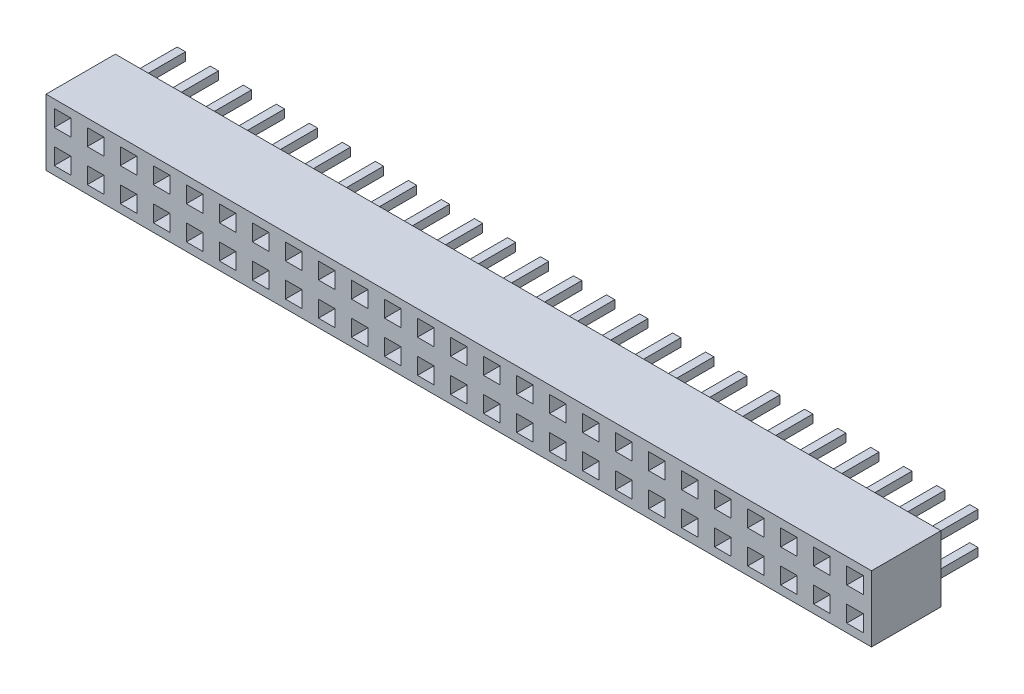
SolidWorks part; units mm, degrees
material "黄銅"
ref_plane "正面" through (0, 0, 0) normal (0, 0, 1) x (1, 0, 0)
ref_plane "平面" through (0, 0, 0) normal (0, 1, 0) x (1, 0, 0)
ref_plane "右側面" through (0, 0, 0) normal (1, 0, 0) x (0, 0, -1)
sketch "Sketch1" plane through (0, 0, 0) normal (0, 0, 1) x (1, 0, 0)
  line L1 (-25, 2) -> (25, 2)
  line L2 (-25, 2) -> (-25, -2)
  line L3 (-25, -2) -> (25, -2)
  line L4 (25, 2) -> (25, -2)
  line L5 (-25, 2) -> (25, -2) construction
  line L6 (-25, -2) -> (25, 2) construction
  point P0 (0, 0)
  dimension "D1" = 50
  dimension "D2" = 4
extrude "Boss-Extrude1" add sketch "Sketch1" along normal blind 4.2
sketch "Sketch3" plane through (0, 0, 4.2) normal (0, 0, 1) x (1, 0, 0)
  line L0 (25, 2) -> (-25, 2) construction
  line L1 (-24.5, 1.5) -> (-23.5, 1.5)
  line L2 (-24.5, 1.5) -> (-24.5, 0.5)
  line L3 (-24.5, 0.5) -> (-23.5, 0.5)
  line L4 (-23.5, 1.5) -> (-23.5, 0.5)
  line L5 (-24.5, -0.5) -> (-23.5, -0.5)
  line L6 (-24.5, -0.5) -> (-24.5, -1.5)
  line L7 (-24.5, -1.5) -> (-23.5, -1.5)
  line L8 (-23.5, -0.5) -> (-23.5, -1.5)
  line L9 (-25, 2) -> (-25, -2) construction
  line L10 (-25, -2) -> (25, -2) construction
  line L11 (-21.5, 1.5) -> (-21.5, 0.5)
  line L12 (-22.5, 1.5) -> (-21.5, 1.5)
  line L13 (-22.5, 1.5) -> (-22.5, 0.5)
  line L14 (-22.5, 0.5) -> (-21.5, 0.5)
  line L15 (-19.5, 1.5) -> (-19.5, 0.5)
  line L16 (-20.5, 1.5) -> (-19.5, 1.5)
  line L17 (-20.5, 1.5) -> (-20.5, 0.5)
  line L18 (-20.5, 0.5) -> (-19.5, 0.5)
  line L19 (-17.5, 1.5) -> (-17.5, 0.5)
  line L20 (-18.5, 1.5) -> (-17.5, 1.5)
  line L21 (-18.5, 1.5) -> (-18.5, 0.5)
  line L22 (-18.5, 0.5) -> (-17.5, 0.5)
  line L23 (-15.5, 1.5) -> (-15.5, 0.5)
  line L24 (-16.5, 1.5) -> (-15.5, 1.5)
  line L25 (-16.5, 1.5) -> (-16.5, 0.5)
  line L26 (-16.5, 0.5) -> (-15.5, 0.5)
  line L27 (-13.5, 1.5) -> (-13.5, 0.5)
  line L28 (-14.5, 1.5) -> (-13.5, 1.5)
  line L29 (-14.5, 1.5) -> (-14.5, 0.5)
  line L30 (-14.5, 0.5) -> (-13.5, 0.5)
  line L31 (-11.5, 1.5) -> (-11.5, 0.5)
  line L32 (-12.5, 1.5) -> (-11.5, 1.5)
  line L33 (-12.5, 1.5) -> (-12.5, 0.5)
  line L34 (-12.5, 0.5) -> (-11.5, 0.5)
  line L35 (-9.5, 1.5) -> (-9.5, 0.5)
  line L36 (-10.5, 1.5) -> (-9.5, 1.5)
  line L37 (-10.5, 1.5) -> (-10.5, 0.5)
  line L38 (-10.5, 0.5) -> (-9.5, 0.5)
  line L39 (-7.5, 1.5) -> (-7.5, 0.5)
  line L40 (-8.5, 1.5) -> (-7.5, 1.5)
  line L41 (-8.5, 1.5) -> (-8.5, 0.5)
  line L42 (-8.5, 0.5) -> (-7.5, 0.5)
  line L43 (-5.5, 1.5) -> (-5.5, 0.5)
  line L44 (-6.5, 1.5) -> (-5.5, 1.5)
  line L45 (-6.5, 1.5) -> (-6.5, 0.5)
  line L46 (-6.5, 0.5) -> (-5.5, 0.5)
  line L47 (-3.5, 1.5) -> (-3.5, 0.5)
  line L48 (-4.5, 1.5) -> (-3.5, 1.5)
  line L49 (-4.5, 1.5) -> (-4.5, 0.5)
  line L50 (-4.5, 0.5) -> (-3.5, 0.5)
  line L51 (-1.5, 1.5) -> (-1.5, 0.5)
  line L52 (-2.5, 1.5) -> (-1.5, 1.5)
  line L53 (-2.5, 1.5) -> (-2.5, 0.5)
  line L54 (-2.5, 0.5) -> (-1.5, 0.5)
  line L55 (0.5, 1.5) -> (0.5, 0.5)
  line L56 (-0.5, 1.5) -> (0.5, 1.5)
  line L57 (-0.5, 1.5) -> (-0.5, 0.5)
  line L58 (-0.5, 0.5) -> (0.5, 0.5)
  line L59 (2.5, 1.5) -> (2.5, 0.5)
  line L60 (1.5, 1.5) -> (2.5, 1.5)
  line L61 (1.5, 1.5) -> (1.5, 0.5)
  line L62 (1.5, 0.5) -> (2.5, 0.5)
  line L63 (4.5, 1.5) -> (4.5, 0.5)
  line L64 (3.5, 1.5) -> (4.5, 1.5)
  line L65 (3.5, 1.5) -> (3.5, 0.5)
  line L66 (3.5, 0.5) -> (4.5, 0.5)
  line L67 (6.5, 1.5) -> (6.5, 0.5)
  line L68 (5.5, 1.5) -> (6.5, 1.5)
  line L69 (5.5, 1.5) -> (5.5, 0.5)
  line L70 (5.5, 0.5) -> (6.5, 0.5)
  line L71 (8.5, 1.5) -> (8.5, 0.5)
  line L72 (7.5, 1.5) -> (8.5, 1.5)
  line L73 (7.5, 1.5) -> (7.5, 0.5)
  line L74 (7.5, 0.5) -> (8.5, 0.5)
  line L75 (10.5, 1.5) -> (10.5, 0.5)
  line L76 (9.5, 1.5) -> (10.5, 1.5)
  line L77 (9.5, 1.5) -> (9.5, 0.5)
  line L78 (9.5, 0.5) -> (10.5, 0.5)
  line L79 (12.5, 1.5) -> (12.5, 0.5)
  line L80 (11.5, 1.5) -> (12.5, 1.5)
  line L81 (11.5, 1.5) -> (11.5, 0.5)
  line L82 (11.5, 0.5) -> (12.5, 0.5)
  line L83 (14.5, 1.5) -> (14.5, 0.5)
  line L84 (13.5, 1.5) -> (14.5, 1.5)
  line L85 (13.5, 1.5) -> (13.5, 0.5)
  line L86 (13.5, 0.5) -> (14.5, 0.5)
  line L87 (16.5, 1.5) -> (16.5, 0.5)
  line L88 (15.5, 1.5) -> (16.5, 1.5)
  line L89 (15.5, 1.5) -> (15.5, 0.5)
  line L90 (15.5, 0.5) -> (16.5, 0.5)
  line L91 (18.5, 1.5) -> (18.5, 0.5)
  line L92 (17.5, 1.5) -> (18.5, 1.5)
  line L93 (17.5, 1.5) -> (17.5, 0.5)
  line L94 (17.5, 0.5) -> (18.5, 0.5)
  line L95 (20.5, 1.5) -> (20.5, 0.5)
  line L96 (19.5, 1.5) -> (20.5, 1.5)
  line L97 (19.5, 1.5) -> (19.5, 0.5)
  line L98 (19.5, 0.5) -> (20.5, 0.5)
  line L99 (22.5, 1.5) -> (22.5, 0.5)
  line L100 (21.5, 1.5) -> (22.5, 1.5)
  line L101 (21.5, 1.5) -> (21.5, 0.5)
  line L102 (21.5, 0.5) -> (22.5, 0.5)
  line L103 (24.5, 1.5) -> (24.5, 0.5)
  line L104 (23.5, 1.5) -> (24.5, 1.5)
  line L105 (23.5, 1.5) -> (23.5, 0.5)
  line L106 (23.5, 0.5) -> (24.5, 0.5)
  line L107 (-21.5, -0.5) -> (-21.5, -1.5)
  line L108 (-22.5, -1.5) -> (-21.5, -1.5)
  line L109 (-22.5, -0.5) -> (-22.5, -1.5)
  line L110 (-22.5, -0.5) -> (-21.5, -0.5)
  line L111 (-19.5, -0.5) -> (-19.5, -1.5)
  line L112 (-20.5, -1.5) -> (-19.5, -1.5)
  line L113 (-20.5, -0.5) -> (-20.5, -1.5)
  line L114 (-20.5, -0.5) -> (-19.5, -0.5)
  line L115 (-17.5, -0.5) -> (-17.5, -1.5)
  line L116 (-18.5, -1.5) -> (-17.5, -1.5)
  line L117 (-18.5, -0.5) -> (-18.5, -1.5)
  line L118 (-18.5, -0.5) -> (-17.5, -0.5)
  line L119 (-15.5, -0.5) -> (-15.5, -1.5)
  line L120 (-16.5, -1.5) -> (-15.5, -1.5)
  line L121 (-16.5, -0.5) -> (-16.5, -1.5)
  line L122 (-16.5, -0.5) -> (-15.5, -0.5)
  line L123 (-13.5, -0.5) -> (-13.5, -1.5)
  line L124 (-14.5, -1.5) -> (-13.5, -1.5)
  line L125 (-14.5, -0.5) -> (-14.5, -1.5)
  line L126 (-14.5, -0.5) -> (-13.5, -0.5)
  line L127 (-11.5, -0.5) -> (-11.5, -1.5)
  line L128 (-12.5, -1.5) -> (-11.5, -1.5)
  line L129 (-12.5, -0.5) -> (-12.5, -1.5)
  line L130 (-12.5, -0.5) -> (-11.5, -0.5)
  line L131 (-9.5, -0.5) -> (-9.5, -1.5)
  line L132 (-10.5, -1.5) -> (-9.5, -1.5)
  line L133 (-10.5, -0.5) -> (-10.5, -1.5)
  line L134 (-10.5, -0.5) -> (-9.5, -0.5)
  line L135 (-7.5, -0.5) -> (-7.5, -1.5)
  line L136 (-8.5, -1.5) -> (-7.5, -1.5)
  line L137 (-8.5, -0.5) -> (-8.5, -1.5)
  line L138 (-8.5, -0.5) -> (-7.5, -0.5)
  line L139 (-5.5, -0.5) -> (-5.5, -1.5)
  line L140 (-6.5, -1.5) -> (-5.5, -1.5)
  line L141 (-6.5, -0.5) -> (-6.5, -1.5)
  line L142 (-6.5, -0.5) -> (-5.5, -0.5)
  line L143 (-3.5, -0.5) -> (-3.5, -1.5)
  line L144 (-4.5, -1.5) -> (-3.5, -1.5)
  line L145 (-4.5, -0.5) -> (-4.5, -1.5)
  line L146 (-4.5, -0.5) -> (-3.5, -0.5)
  line L147 (-1.5, -0.5) -> (-1.5, -1.5)
  line L148 (-2.5, -1.5) -> (-1.5, -1.5)
  line L149 (-2.5, -0.5) -> (-2.5, -1.5)
  line L150 (-2.5, -0.5) -> (-1.5, -0.5)
  line L151 (0.5, -0.5) -> (0.5, -1.5)
  line L152 (-0.5, -1.5) -> (0.5, -1.5)
  line L153 (-0.5, -0.5) -> (-0.5, -1.5)
  line L154 (-0.5, -0.5) -> (0.5, -0.5)
  line L155 (2.5, -0.5) -> (2.5, -1.5)
  line L156 (1.5, -1.5) -> (2.5, -1.5)
  line L157 (1.5, -0.5) -> (1.5, -1.5)
  line L158 (1.5, -0.5) -> (2.5, -0.5)
  line L159 (4.5, -0.5) -> (4.5, -1.5)
  line L160 (3.5, -1.5) -> (4.5, -1.5)
  line L161 (3.5, -0.5) -> (3.5, -1.5)
  line L162 (3.5, -0.5) -> (4.5, -0.5)
  line L163 (6.5, -0.5) -> (6.5, -1.5)
  line L164 (5.5, -1.5) -> (6.5, -1.5)
  line L165 (5.5, -0.5) -> (5.5, -1.5)
  line L166 (5.5, -0.5) -> (6.5, -0.5)
  line L167 (8.5, -0.5) -> (8.5, -1.5)
  line L168 (7.5, -1.5) -> (8.5, -1.5)
  line L169 (7.5, -0.5) -> (7.5, -1.5)
  line L170 (7.5, -0.5) -> (8.5, -0.5)
  line L171 (10.5, -0.5) -> (10.5, -1.5)
  line L172 (9.5, -1.5) -> (10.5, -1.5)
  line L173 (9.5, -0.5) -> (9.5, -1.5)
  line L174 (9.5, -0.5) -> (10.5, -0.5)
  line L175 (12.5, -0.5) -> (12.5, -1.5)
  line L176 (11.5, -1.5) -> (12.5, -1.5)
  line L177 (11.5, -0.5) -> (11.5, -1.5)
  line L178 (11.5, -0.5) -> (12.5, -0.5)
  line L179 (14.5, -0.5) -> (14.5, -1.5)
  line L180 (13.5, -1.5) -> (14.5, -1.5)
  line L181 (13.5, -0.5) -> (13.5, -1.5)
  line L182 (13.5, -0.5) -> (14.5, -0.5)
  line L183 (16.5, -0.5) -> (16.5, -1.5)
  line L184 (15.5, -1.5) -> (16.5, -1.5)
  line L185 (15.5, -0.5) -> (15.5, -1.5)
  line L186 (15.5, -0.5) -> (16.5, -0.5)
  line L187 (18.5, -0.5) -> (18.5, -1.5)
  line L188 (17.5, -1.5) -> (18.5, -1.5)
  line L189 (17.5, -0.5) -> (17.5, -1.5)
  line L190 (17.5, -0.5) -> (18.5, -0.5)
  line L191 (20.5, -0.5) -> (20.5, -1.5)
  line L192 (19.5, -1.5) -> (20.5, -1.5)
  line L193 (19.5, -0.5) -> (19.5, -1.5)
  line L194 (19.5, -0.5) -> (20.5, -0.5)
  line L195 (22.5, -0.5) -> (22.5, -1.5)
  line L196 (21.5, -1.5) -> (22.5, -1.5)
  line L197 (21.5, -0.5) -> (21.5, -1.5)
  line L198 (21.5, -0.5) -> (22.5, -0.5)
  line L199 (24.5, -0.5) -> (24.5, -1.5)
  line L200 (23.5, -1.5) -> (24.5, -1.5)
  line L201 (23.5, -0.5) -> (23.5, -1.5)
  line L202 (23.5, -0.5) -> (24.5, -0.5)
  dimension "D1" = 1
  dimension "D2" = 1
  dimension "D3" = 0.5
  dimension "D4" = 0.5
  dimension "D5" = 1
  dimension "D6" = 1
  dimension "D7" = 0.5
  dimension "D8" = 0.5
extrude "Cut-Extrude1" cut sketch "Sketch3" against normal blind 3
sketch "Sketch4" plane through (0, 0, 0) normal (0, 0, -1) x (-1, 0, 0)
  line L0 (-25, 2) -> (25, 2) construction
  line L1 (-24.25, 1.25) -> (-23.75, 1.25)
  line L2 (-24.25, 1.25) -> (-24.25, 0.75)
  line L3 (-24.25, 0.75) -> (-23.75, 0.75)
  line L4 (-23.75, 1.25) -> (-23.75, 0.75)
  line L5 (-24.25, -0.75) -> (-23.75, -0.75)
  line L6 (-24.25, -0.75) -> (-24.25, -1.25)
  line L7 (-24.25, -1.25) -> (-23.75, -1.25)
  line L8 (-23.75, -0.75) -> (-23.75, -1.25)
  line L9 (-25, -2) -> (-25, 2) construction
  line L10 (25, -2) -> (-25, -2) construction
  line L11 (-22.25, -0.75) -> (-22.25, -1.25)
  line L12 (-22.25, -1.25) -> (-21.75, -1.25)
  line L13 (-21.75, -0.75) -> (-21.75, -1.25)
  line L14 (-22.25, -0.75) -> (-21.75, -0.75)
  line L15 (-22.25, 0.75) -> (-21.75, 0.75)
  line L16 (-22.25, 1.25) -> (-21.75, 1.25)
  line L17 (-22.25, 1.25) -> (-22.25, 0.75)
  line L18 (-21.75, 1.25) -> (-21.75, 0.75)
  line L19 (-20.25, -0.75) -> (-20.25, -1.25)
  line L20 (-20.25, -1.25) -> (-19.75, -1.25)
  line L21 (-19.75, -0.75) -> (-19.75, -1.25)
  line L22 (-20.25, -0.75) -> (-19.75, -0.75)
  line L23 (-20.25, 0.75) -> (-19.75, 0.75)
  line L24 (-20.25, 1.25) -> (-19.75, 1.25)
  line L25 (-20.25, 1.25) -> (-20.25, 0.75)
  line L26 (-19.75, 1.25) -> (-19.75, 0.75)
  line L27 (-18.25, -0.75) -> (-18.25, -1.25)
  line L28 (-18.25, -1.25) -> (-17.75, -1.25)
  line L29 (-17.75, -0.75) -> (-17.75, -1.25)
  line L30 (-18.25, -0.75) -> (-17.75, -0.75)
  line L31 (-18.25, 0.75) -> (-17.75, 0.75)
  line L32 (-18.25, 1.25) -> (-17.75, 1.25)
  line L33 (-18.25, 1.25) -> (-18.25, 0.75)
  line L34 (-17.75, 1.25) -> (-17.75, 0.75)
  line L35 (-16.25, -0.75) -> (-16.25, -1.25)
  line L36 (-16.25, -1.25) -> (-15.75, -1.25)
  line L37 (-15.75, -0.75) -> (-15.75, -1.25)
  line L38 (-16.25, -0.75) -> (-15.75, -0.75)
  line L39 (-16.25, 0.75) -> (-15.75, 0.75)
  line L40 (-16.25, 1.25) -> (-15.75, 1.25)
  line L41 (-16.25, 1.25) -> (-16.25, 0.75)
  line L42 (-15.75, 1.25) -> (-15.75, 0.75)
  line L43 (-14.25, -0.75) -> (-14.25, -1.25)
  line L44 (-14.25, -1.25) -> (-13.75, -1.25)
  line L45 (-13.75, -0.75) -> (-13.75, -1.25)
  line L46 (-14.25, -0.75) -> (-13.75, -0.75)
  line L47 (-14.25, 0.75) -> (-13.75, 0.75)
  line L48 (-14.25, 1.25) -> (-13.75, 1.25)
  line L49 (-14.25, 1.25) -> (-14.25, 0.75)
  line L50 (-13.75, 1.25) -> (-13.75, 0.75)
  line L51 (-12.25, -0.75) -> (-12.25, -1.25)
  line L52 (-12.25, -1.25) -> (-11.75, -1.25)
  line L53 (-11.75, -0.75) -> (-11.75, -1.25)
  line L54 (-12.25, -0.75) -> (-11.75, -0.75)
  line L55 (-12.25, 0.75) -> (-11.75, 0.75)
  line L56 (-12.25, 1.25) -> (-11.75, 1.25)
  line L57 (-12.25, 1.25) -> (-12.25, 0.75)
  line L58 (-11.75, 1.25) -> (-11.75, 0.75)
  line L59 (-10.25, -0.75) -> (-10.25, -1.25)
  line L60 (-10.25, -1.25) -> (-9.75, -1.25)
  line L61 (-9.75, -0.75) -> (-9.75, -1.25)
  line L62 (-10.25, -0.75) -> (-9.75, -0.75)
  line L63 (-10.25, 0.75) -> (-9.75, 0.75)
  line L64 (-10.25, 1.25) -> (-9.75, 1.25)
  line L65 (-10.25, 1.25) -> (-10.25, 0.75)
  line L66 (-9.75, 1.25) -> (-9.75, 0.75)
  line L67 (-8.25, -0.75) -> (-8.25, -1.25)
  line L68 (-8.25, -1.25) -> (-7.75, -1.25)
  line L69 (-7.75, -0.75) -> (-7.75, -1.25)
  line L70 (-8.25, -0.75) -> (-7.75, -0.75)
  line L71 (-8.25, 0.75) -> (-7.75, 0.75)
  line L72 (-8.25, 1.25) -> (-7.75, 1.25)
  line L73 (-8.25, 1.25) -> (-8.25, 0.75)
  line L74 (-7.75, 1.25) -> (-7.75, 0.75)
  line L75 (-6.25, -0.75) -> (-6.25, -1.25)
  line L76 (-6.25, -1.25) -> (-5.75, -1.25)
  line L77 (-5.75, -0.75) -> (-5.75, -1.25)
  line L78 (-6.25, -0.75) -> (-5.75, -0.75)
  line L79 (-6.25, 0.75) -> (-5.75, 0.75)
  line L80 (-6.25, 1.25) -> (-5.75, 1.25)
  line L81 (-6.25, 1.25) -> (-6.25, 0.75)
  line L82 (-5.75, 1.25) -> (-5.75, 0.75)
  line L83 (-4.25, -0.75) -> (-4.25, -1.25)
  line L84 (-4.25, -1.25) -> (-3.75, -1.25)
  line L85 (-3.75, -0.75) -> (-3.75, -1.25)
  line L86 (-4.25, -0.75) -> (-3.75, -0.75)
  line L87 (-4.25, 0.75) -> (-3.75, 0.75)
  line L88 (-4.25, 1.25) -> (-3.75, 1.25)
  line L89 (-4.25, 1.25) -> (-4.25, 0.75)
  line L90 (-3.75, 1.25) -> (-3.75, 0.75)
  line L91 (-2.25, -0.75) -> (-2.25, -1.25)
  line L92 (-2.25, -1.25) -> (-1.75, -1.25)
  line L93 (-1.75, -0.75) -> (-1.75, -1.25)
  line L94 (-2.25, -0.75) -> (-1.75, -0.75)
  line L95 (-2.25, 0.75) -> (-1.75, 0.75)
  line L96 (-2.25, 1.25) -> (-1.75, 1.25)
  line L97 (-2.25, 1.25) -> (-2.25, 0.75)
  line L98 (-1.75, 1.25) -> (-1.75, 0.75)
  line L99 (-0.25, -0.75) -> (-0.25, -1.25)
  line L100 (-0.25, -1.25) -> (0.25, -1.25)
  line L101 (0.25, -0.75) -> (0.25, -1.25)
  line L102 (-0.25, -0.75) -> (0.25, -0.75)
  line L103 (-0.25, 0.75) -> (0.25, 0.75)
  line L104 (-0.25, 1.25) -> (0.25, 1.25)
  line L105 (-0.25, 1.25) -> (-0.25, 0.75)
  line L106 (0.25, 1.25) -> (0.25, 0.75)
  line L107 (1.75, -0.75) -> (1.75, -1.25)
  line L108 (1.75, -1.25) -> (2.25, -1.25)
  line L109 (2.25, -0.75) -> (2.25, -1.25)
  line L110 (1.75, -0.75) -> (2.25, -0.75)
  line L111 (1.75, 0.75) -> (2.25, 0.75)
  line L112 (1.75, 1.25) -> (2.25, 1.25)
  line L113 (1.75, 1.25) -> (1.75, 0.75)
  line L114 (2.25, 1.25) -> (2.25, 0.75)
  line L115 (3.75, -0.75) -> (3.75, -1.25)
  line L116 (3.75, -1.25) -> (4.25, -1.25)
  line L117 (4.25, -0.75) -> (4.25, -1.25)
  line L118 (3.75, -0.75) -> (4.25, -0.75)
  line L119 (3.75, 0.75) -> (4.25, 0.75)
  line L120 (3.75, 1.25) -> (4.25, 1.25)
  line L121 (3.75, 1.25) -> (3.75, 0.75)
  line L122 (4.25, 1.25) -> (4.25, 0.75)
  line L123 (5.75, -0.75) -> (5.75, -1.25)
  line L124 (5.75, -1.25) -> (6.25, -1.25)
  line L125 (6.25, -0.75) -> (6.25, -1.25)
  line L126 (5.75, -0.75) -> (6.25, -0.75)
  line L127 (5.75, 0.75) -> (6.25, 0.75)
  line L128 (5.75, 1.25) -> (6.25, 1.25)
  line L129 (5.75, 1.25) -> (5.75, 0.75)
  line L130 (6.25, 1.25) -> (6.25, 0.75)
  line L131 (7.75, -0.75) -> (7.75, -1.25)
  line L132 (7.75, -1.25) -> (8.25, -1.25)
  line L133 (8.25, -0.75) -> (8.25, -1.25)
  line L134 (7.75, -0.75) -> (8.25, -0.75)
  line L135 (7.75, 0.75) -> (8.25, 0.75)
  line L136 (7.75, 1.25) -> (8.25, 1.25)
  line L137 (7.75, 1.25) -> (7.75, 0.75)
  line L138 (8.25, 1.25) -> (8.25, 0.75)
  line L139 (9.75, -0.75) -> (9.75, -1.25)
  line L140 (9.75, -1.25) -> (10.25, -1.25)
  line L141 (10.25, -0.75) -> (10.25, -1.25)
  line L142 (9.75, -0.75) -> (10.25, -0.75)
  line L143 (9.75, 0.75) -> (10.25, 0.75)
  line L144 (9.75, 1.25) -> (10.25, 1.25)
  line L145 (9.75, 1.25) -> (9.75, 0.75)
  line L146 (10.25, 1.25) -> (10.25, 0.75)
  line L147 (11.75, -0.75) -> (11.75, -1.25)
  line L148 (11.75, -1.25) -> (12.25, -1.25)
  line L149 (12.25, -0.75) -> (12.25, -1.25)
  line L150 (11.75, -0.75) -> (12.25, -0.75)
  line L151 (11.75, 0.75) -> (12.25, 0.75)
  line L152 (11.75, 1.25) -> (12.25, 1.25)
  line L153 (11.75, 1.25) -> (11.75, 0.75)
  line L154 (12.25, 1.25) -> (12.25, 0.75)
  line L155 (13.75, -0.75) -> (13.75, -1.25)
  line L156 (13.75, -1.25) -> (14.25, -1.25)
  line L157 (14.25, -0.75) -> (14.25, -1.25)
  line L158 (13.75, -0.75) -> (14.25, -0.75)
  line L159 (13.75, 0.75) -> (14.25, 0.75)
  line L160 (13.75, 1.25) -> (14.25, 1.25)
  line L161 (13.75, 1.25) -> (13.75, 0.75)
  line L162 (14.25, 1.25) -> (14.25, 0.75)
  line L163 (15.75, -0.75) -> (15.75, -1.25)
  line L164 (15.75, -1.25) -> (16.25, -1.25)
  line L165 (16.25, -0.75) -> (16.25, -1.25)
  line L166 (15.75, -0.75) -> (16.25, -0.75)
  line L167 (15.75, 0.75) -> (16.25, 0.75)
  line L168 (15.75, 1.25) -> (16.25, 1.25)
  line L169 (15.75, 1.25) -> (15.75, 0.75)
  line L170 (16.25, 1.25) -> (16.25, 0.75)
  line L171 (17.75, -0.75) -> (17.75, -1.25)
  line L172 (17.75, -1.25) -> (18.25, -1.25)
  line L173 (18.25, -0.75) -> (18.25, -1.25)
  line L174 (17.75, -0.75) -> (18.25, -0.75)
  line L175 (17.75, 0.75) -> (18.25, 0.75)
  line L176 (17.75, 1.25) -> (18.25, 1.25)
  line L177 (17.75, 1.25) -> (17.75, 0.75)
  line L178 (18.25, 1.25) -> (18.25, 0.75)
  line L179 (19.75, -0.75) -> (19.75, -1.25)
  line L180 (19.75, -1.25) -> (20.25, -1.25)
  line L181 (20.25, -0.75) -> (20.25, -1.25)
  line L182 (19.75, -0.75) -> (20.25, -0.75)
  line L183 (19.75, 0.75) -> (20.25, 0.75)
  line L184 (19.75, 1.25) -> (20.25, 1.25)
  line L185 (19.75, 1.25) -> (19.75, 0.75)
  line L186 (20.25, 1.25) -> (20.25, 0.75)
  line L187 (21.75, -0.75) -> (21.75, -1.25)
  line L188 (21.75, -1.25) -> (22.25, -1.25)
  line L189 (22.25, -0.75) -> (22.25, -1.25)
  line L190 (21.75, -0.75) -> (22.25, -0.75)
  line L191 (21.75, 0.75) -> (22.25, 0.75)
  line L192 (21.75, 1.25) -> (22.25, 1.25)
  line L193 (21.75, 1.25) -> (21.75, 0.75)
  line L194 (22.25, 1.25) -> (22.25, 0.75)
  line L195 (23.75, -0.75) -> (23.75, -1.25)
  line L196 (23.75, -1.25) -> (24.25, -1.25)
  line L197 (24.25, -0.75) -> (24.25, -1.25)
  line L198 (23.75, -0.75) -> (24.25, -0.75)
  line L199 (23.75, 0.75) -> (24.25, 0.75)
  line L200 (23.75, 1.25) -> (24.25, 1.25)
  line L201 (23.75, 1.25) -> (23.75, 0.75)
  line L202 (24.25, 1.25) -> (24.25, 0.75)
  dimension "D1" = 0.5
  dimension "D2" = 0.5
  dimension "D3" = 0.75
  dimension "D4" = 0.75
  dimension "D5" = 0.5
  dimension "D6" = 0.5
  dimension "D7" = 0.75
  dimension "D8" = 0.75
extrude "Boss-Extrude2" add sketch "Sketch4" along normal blind 3
sketch "Sketch5" plane through (0, 0, 4.2) normal (0, 0, 1) x (1, 0, 0)
  line L0 (0, -9.815) -> (0, 17.2074) construction
equation "\"7.5.00mm\"=75"
